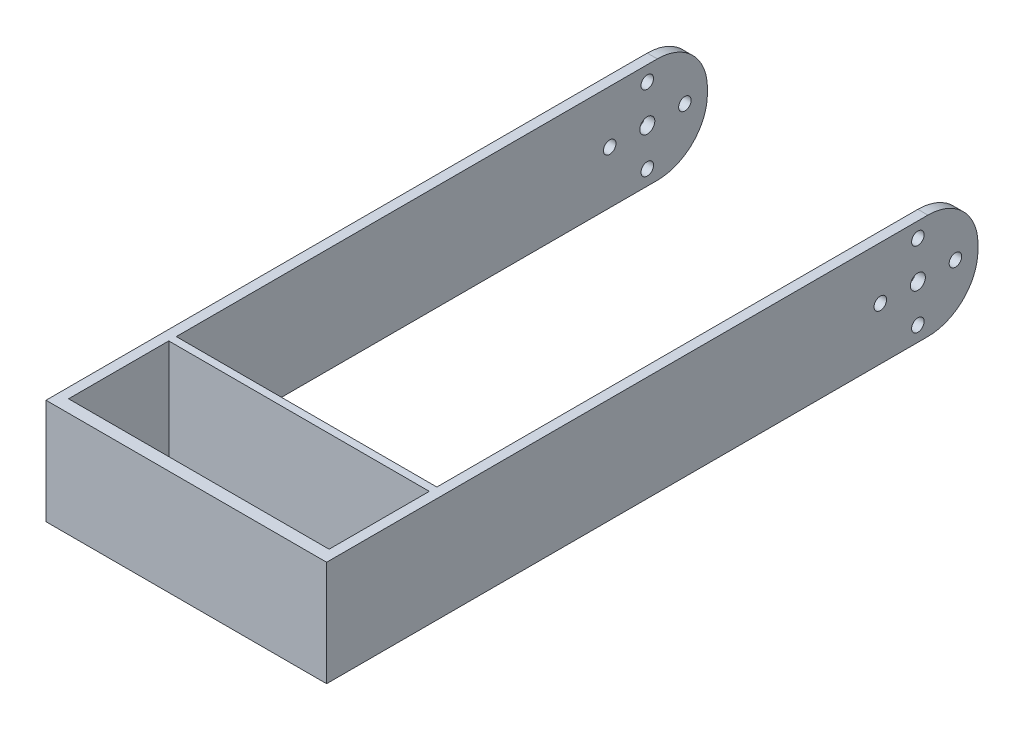
SolidWorks part; units mm, degrees
ref_plane "Front Plane" through (0, 0, 0) normal (0, 0, 1) x (1, 0, 0)
ref_plane "Top Plane" through (0, 0, 0) normal (0, 1, 0) x (1, 0, 0)
ref_plane "Right Plane" through (0, 0, 0) normal (1, 0, 0) x (0, 0, -1)
sketch "Sketch3" plane through (0, 0, 0) normal (0, 0, 1) x (1, 0, 0)
  line L1 (-28, 10.5) -> (28, 10.5)
  line L2 (-28, 10.5) -> (-28, -10.5)
  line L3 (-28, -10.5) -> (28, -10.5)
  line L4 (28, 10.5) -> (28, -10.5)
  line L5 (-28, 10.5) -> (28, -10.5) construction
  line L6 (-28, -10.5) -> (28, 10.5) construction
  point P0 (0, 0)
  dimension "D1" = 56
  dimension "D2" = 21
extrude "Boss-Extrude1" add sketch "Sketch3" along normal blind 130
sketch "Sketch4" plane through (0, -10.5, 0) normal (0, -1, 0) x (1, 0, 0)
  line L0 (0, 0) -> (0, 35) construction
  line L1 (26, 0) -> (26, 106)
  line L2 (26, 107.5) -> (26, 127.5)
  line L7 (-28, 0) -> (28, 0) construction
  line L8 (26, 127.5) -> (-26, 127.5)
  line L9 (-26, 127.5) -> (-26, 107.5)
  line L10 (-26, 106) -> (-26, 0)
  line L11 (-26, 0) -> (26, 0)
  line L12 (28, 130) -> (28, 0) construction
  line L13 (-28, 130) -> (-28, 0) construction
  line L14 (-28, 130) -> (28, 130) construction
  line L15 (-26, 107.5) -> (26, 107.5)
  line L16 (-26, 106) -> (26, 106)
  dimension "D1" = 35
  dimension "D2" = 2
  dimension "D3" = 2
  dimension "D4" = 2.5
  dimension "D5" = 1.5
  dimension "D6" = 20
extrude "Cut-Extrude3" cut sketch "Sketch4" against normal through all
sketch "Sketch6" plane through (28, 0, 0) normal (1, 0, 0) x (0, 0, -1)
  line L0 (0, -10.5) -> (0, 10.5) construction
  line L1 (0, 0) -> (-22.8922, 0) construction
  line L2 (-12, 0) -> (-12, 9.1156) construction
  line L3 (-12, 0) -> (-12, 6.3751) construction
  circle A0 centre (-12, 0) radius 1.5
  circle A7 centre (-4.5, 0) radius 1.25
  circle A8 centre (-19.5, 0) radius 1.25
  circle A9 centre (-12, 7.5) radius 1.25
  circle A10 centre (-12, -7.5) radius 1.25
  point P19 (-9, 0)
  dimension "D1" = 12
  dimension "D2" = 3
  dimension "D3" = 2.5
  dimension "D4" = 7.5
  dimension "D5" = 2.5
  dimension "D6" = 7.5
extrude "Cut-Extrude4" cut sketch "Sketch6" against normal through all
fillet "Fillet1" radius 10 4 edges at (27, 10.5, 0) (27, -10.5, 0) (-27, 10.5, 0) (-27, -10.5, 0)
